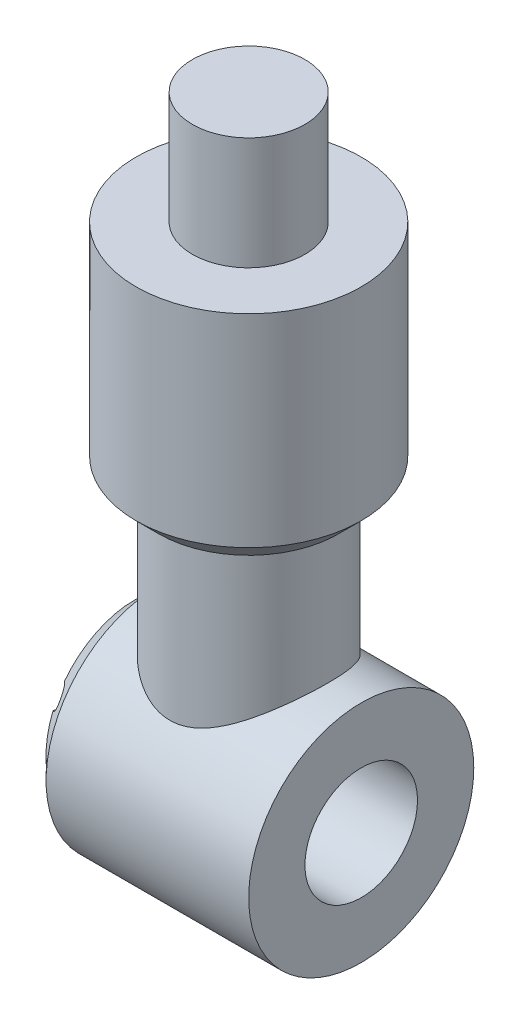
SolidWorks part; units mm, degrees
ref_plane "Front Plane" through (0, 0, 0) normal (0, 0, 1) x (1, 0, 0)
ref_plane "Top Plane" through (0, 0, 0) normal (0, 1, 0) x (1, 0, 0)
ref_plane "Right Plane" through (0, 0, 0) normal (1, 0, 0) x (0, 0, -1)
sketch "Sketch1" plane through (0, 0, 0) normal (0, 1, 0) x (1, 0, 0)
  circle A0 centre (0, 0) radius 88.9
  dimension "D1" = 177.8
extrude "Boss-Extrude1" add sketch "Sketch1" along normal mid plane 203.2
sketch "Sketch4" plane through (0, 0, 0) normal (1, 0, 0) x (0, 0, -1)
  line L2 (0, -101.6) -> (0, -254)
  line L3 (-88.9, -101.6) -> (88.9, -101.6) construction
  circle A1 centre (0, -177.8) radius 127
  dimension "D4" = 254
  dimension "D3" = 152.4
extrude "Boss-Extrude2" add sketch "Sketch4" along normal mid plane 254
sketch "Sketch5" plane through (127, 0, 0) normal (1, 0, 0) x (0, 0, -1)
  circle A0 centre (0, -177.8) radius 63.5
  circle A1 centre (0, -177.8) radius 127 construction
  dimension "D2" = 127
  dimension "D1" = 63.5
sketch "Sketch6" plane through (0, 101.6, 0) normal (0, 1, 0) x (1, 0, 0)
  circle A0 centre (0, 0) radius 127
  circle A1 centre (0, 0) radius 88.9 construction
  dimension "D2" = 254
  dimension "D1" = 38.1
extrude "Boss-Extrude4" add sketch "Sketch6" along normal blind 254
extrude "Cut-Extrude1" cut sketch "Sketch5" against normal blind 127
sketch "Sketch7" plane through (0, 355.6, 0) normal (0, 1, 0) x (1, 0, 0)
  circle A0 centre (0, 0) radius 63.5
  dimension "D1" = 127
extrude "Boss-Extrude5" add sketch "Sketch7" along normal blind 127
chamfer "Chamfer1" distance 25.4 angle 45 1 edges at (-127, -177.8, -127)
sketch "Sketch8" plane through (-127, 0, 0) normal (-1, 0, 0) x (0, 0, 1)
  circle A0 centre (0, -76.2) radius 12.7
  circle A1 centre (0, -177.8) radius 101.6 construction
  circle A2 centre (87.9882, -127) radius 12.7
  circle A3 centre (87.9882, -228.6) radius 12.7
  circle A4 centre (0, -279.4) radius 12.7
  circle A5 centre (-87.9882, -228.6) radius 12.7
  circle A6 centre (-87.9882, -127) radius 12.7
  point P16 (0, -177.8)
  dimension "D1" = 25.4
  dimension "D2" = 6
extrude "Cut-Extrude2" cut sketch "Sketch8" against normal blind 25.4
chamfer "Chamfer2" distance 25.4 angle 45 1 edges at (0, 101.6, 127)
